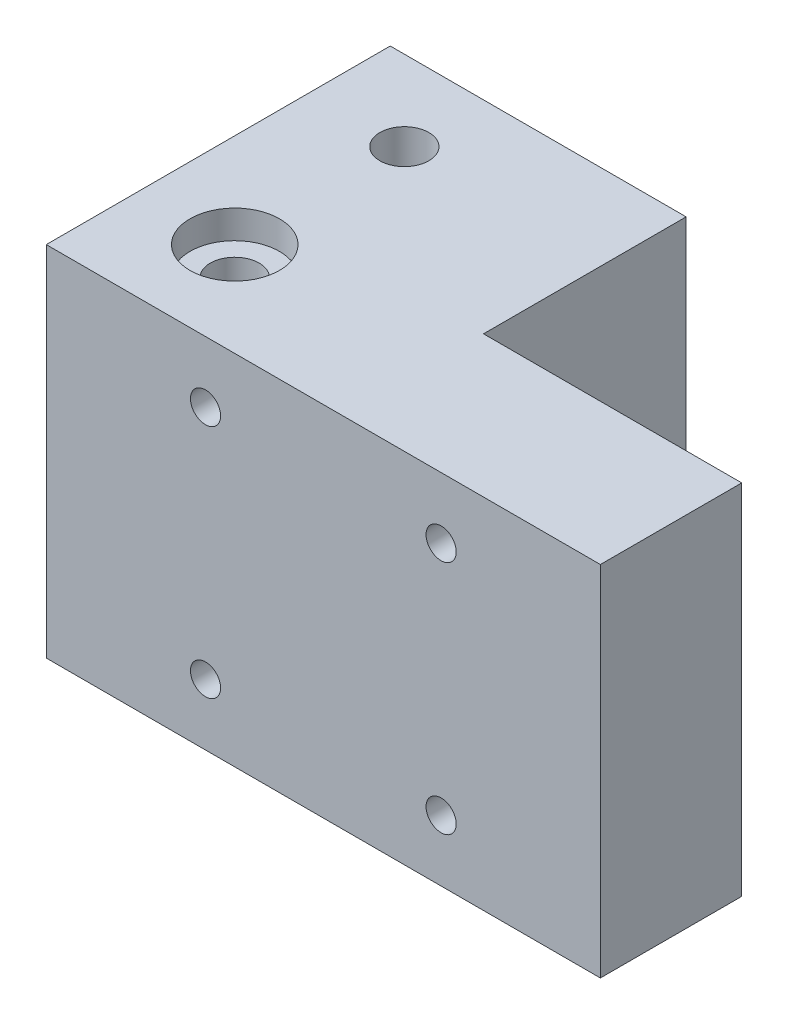
SolidWorks part; units mm, degrees
ref_plane "前视基准面" through (0, 0, 0) normal (0, 0, 1) x (1, 0, 0)
ref_plane "上视基准面" through (0, 0, 0) normal (0, 1, 0) x (1, 0, 0)
ref_plane "右视基准面" through (0, 0, 0) normal (1, 0, 0) x (0, 0, -1)
sketch "草图1" plane through (0, 0, 0) normal (0, 0, 1) x (1, 0, 0)
  line L1 (-30.1396, 19.0453) -> (28.6604, 19.0453)
  line L2 (-30.1396, 19.0453) -> (-30.1396, -12.9547)
  line L3 (-30.1396, -12.9547) -> (28.6604, -12.9547)
  line L4 (28.6604, 19.0453) -> (28.6604, -12.9547)
  dimension "D1" = 58.8
  dimension "D2" = 32
extrude "凸台-拉伸1" add sketch "草图1" along normal blind 41.5
sketch "草图2" plane through (0, 0, 0) normal (0, 0, -1) x (-1, 0, 0)
  line L0 (0.7396, 22.9513) -> (0.7396, -20.038)
  line L1 (42.4969, 3.0453) -> (-36.3492, 3.0453)
  line L2 (-33.9501, -9.4547) -> (38.801, -9.4547)
  line L3 (-33.9501, 15.5453) -> (36.9207, 15.5453)
  line L4 (13.2396, -16.5366) -> (13.2396, 23.8591)
  line L5 (-11.7604, -18.0927) -> (-11.7604, 23.4052)
  dimension "D1" = 12.5
  dimension "D2" = 12.5
  dimension "D3" = 12.5
  dimension "D4" = 12.5
hole_wizard "孔1" positions "3D草图1" profile "草图3" legacy end condition through all
sketch3d "3D草图1"
  line L0 (33.9501, 15.5453, 0) -> (-36.9207, 15.5453, 0) construction
  line L1 (11.7604, -18.0927, 0) -> (11.7604, 23.4052, 0) construction
  line L2 (-13.2396, -16.5366, 0) -> (-13.2396, 23.8591, 0) construction
  line L3 (33.9501, -9.4547, 0) -> (-38.801, -9.4547, 0) construction
  point P0 (11.7604, 15.5453, 0)
  point P6 (-13.2396, 15.5453, 0)
  point P10 (-13.2396, -9.4547, 0)
  point P14 (11.7604, -9.4547, 0)
sketch "草图3" plane through (11.7604, 15.5453, 0) normal (1, 0, 0) x (0, 1, 0)
  line L0 (0, 0) -> (0, 41.5)
  line L1 (0, 41.5) -> (1.6, 41.5)
  line L2 (1.6, 41.5) -> (1.6, 32.5)
  line L3 (1.6, 32.5) -> (3, 32.5)
  line L4 (3, 32.5) -> (3, 0)
  line L5 (3, 0) -> (0, 0)
  line L6 (0, 110) -> (0, -10) construction
  dimension "直径" = 3.2
  dimension "深度" = 41.5
  dimension "柱坑直径" = 6
  dimension "柱坑深度" = 32.5
sketch "草图8" plane through (0, 19.0453, 0) normal (0, 1, 0) x (1, 0, 0)
  circle A0 centre (-0.7396, -31.5) radius 2.6
  dimension "D2" = 5.2
extrude "切除-拉伸6" cut sketch "草图8" against normal blind 33.5
sketch "草图10" plane through (0, -12.9547, 0) normal (0, -1, 0) x (1, 0, 0)
  line L4 (-30.1396, 0) -> (28.6604, 0)
  line L5 (28.6604, 0) -> (28.6604, 41.5)
  line L6 (28.6604, 41.5) -> (-30.1396, 41.5)
  line L7 (-30.1396, 41.5) -> (-30.1396, 0)
  line L8 (-30.1396, 0) -> (28.6604, 0)
  line L9 (28.6604, 0) -> (28.6604, 41.5)
  line L10 (28.6604, 41.5) -> (-30.1396, 41.5)
  line L11 (-30.1396, 41.5) -> (-30.1396, 0)
  dimension "D1" = 0
extrude "凸台-拉伸2" add sketch "草图10" along normal blind 3
sketch "草图18" plane through (0, -12.9547, 0) normal (0, 1, 0) x (1, 0, 0)
  circle A1 centre (-0.7396, -31.5) radius 2.6
  circle A3 centre (-0.7396, -31.5) radius 2.6
  dimension "D1" = 0
extrude "切除-拉伸14" cut sketch "草图18" against normal through all contours A3
sketch "草图19" plane through (0, 0, 0) normal (0, 0, -1) x (-1, 0, 0)
  line L0 (-28.6604, -0.9547) -> (30.1396, -0.9547)
  line L1 (-28.6604, -15.9547) -> (-28.6604, 19.0453) construction
  line L2 (30.1396, 19.0453) -> (30.1396, -15.9547) construction
  line L3 (10.1396, 19.0453) -> (10.1396, -15.9547)
  line L4 (-28.6604, 19.0453) -> (30.1396, 19.0453) construction
  line L5 (30.1396, -15.9547) -> (-28.6604, -15.9547) construction
  line L6 (10.1396, 19.0453) -> (30.1396, 19.0453)
  line L7 (30.1396, 19.0453) -> (30.1396, -0.9547)
  circle M4 centre (13.2396, 15.5453) radius 3
  line M7 (30.1396, -15.9547) -> (30.1396, 19.0453)
  line M8 (30.1396, 19.0453) -> (-28.6604, 19.0453)
  dimension "D1" = 20
  dimension "D2" = 20
extrude "切除-拉伸15" cut sketch "草图19" against normal blind 22 contours L3 L0 M8 M7 M4
sketch "草图20" plane through (0, 0, 0) normal (0, 0, -1) x (-1, 0, 0)
  line L6 (30.1396, -15.9547) -> (30.1396, -0.9547)
  line L7 (30.1396, -0.9547) -> (10.1396, -0.9547)
  line L8 (10.1396, -0.9547) -> (10.1396, 19.0453)
  line L9 (10.1396, 19.0453) -> (-28.6604, 19.0453)
  line L10 (-28.6604, 19.0453) -> (-28.6604, -15.9547)
  line L11 (-28.6604, -15.9547) -> (30.1396, -15.9547)
  line L12 (30.1396, -15.9547) -> (30.1396, -0.9547)
  line L13 (30.1396, -0.9547) -> (10.1396, -0.9547)
  line L14 (10.1396, -0.9547) -> (10.1396, 19.0453)
  line L15 (10.1396, 19.0453) -> (-28.6604, 19.0453)
  line L16 (-28.6604, 19.0453) -> (-28.6604, -15.9547)
  line L17 (-28.6604, -15.9547) -> (30.1396, -15.9547)
  circle A0 centre (13.2396, -9.4547) radius 3 construction
  circle A1 centre (-11.7604, -9.4547) radius 3 construction
  circle A2 centre (-11.7604, 15.5453) radius 3 construction
  circle A3 centre (13.2396, -9.4547) radius 3
  circle A4 centre (-11.7604, -9.4547) radius 3
  circle A5 centre (-11.7604, 15.5453) radius 3
  dimension "D1" = 0
extrude "切除-拉伸16" cut sketch "草图20" against normal blind 5
sketch "草图21" plane through (0, -15.9547, 0) normal (0, -1, 0) x (1, 0, 0)
  line L0 (-30.1396, 19.2146) -> (-17.0647, 5)
  line L1 (-30.1396, 41.5) -> (-30.1396, 5) construction
  line L2 (28.6604, 5) -> (-30.1396, 5) construction
  line L3 (-17.0647, 5) -> (-30.1396, 5)
  line L4 (-30.1396, 5) -> (-30.1396, 19.2146)
extrude "切除-拉伸17" cut sketch "草图21" against normal blind 6
sketch "草图22" plane through (0, 19.0453, 0) normal (0, 1, 0) x (1, 0, 0)
  line L0 (1.2604, -26.5) -> (1.2604, -5)
  line L1 (28.6604, -41.5) -> (-30.1396, -41.5) construction
  line L2 (-10.1396, -5) -> (28.6604, -5) construction
  line L3 (28.6604, -41.5) -> (28.6604, -5) construction
  line L4 (1.2604, -26.5) -> (28.6604, -26.5)
  line L6 (1.2604, -5) -> (28.6604, -5)
  line L7 (28.6604, -5) -> (28.6604, -26.5)
  dimension "D1" = 27.4
  dimension "D2" = 15
extrude "切除-拉伸18" cut sketch "草图22" against normal through all
sketch "草图23" plane through (0, -0.9547, 0) normal (0, 1, 0) x (1, 0, 0)
  circle A0 centre (-20.1396, -13.5) radius 2.6
  dimension "D1" = 5.2
extrude "切除-拉伸19" cut sketch "草图23" against normal through all
sketch "草图24" plane through (0, -15.9547, 0) normal (0, -1, 0) x (-1, 0, 0)
  line L0 (22.7396, -13.5) -> (20.1396, -13.5)
  line L1 (20.1396, -13.5) -> (20.1396, -16.1)
  line L2 (24.6313, -13.2261) -> (20.7871, -9.0468)
  line L3 (17.0647, -5) -> (30.1396, -19.2146) construction
  circle A0 centre (20.1396, -13.5) radius 2.6 construction
  arc A1 (20.7871, -9.0468) -> (24.6313, -13.2261) centre (20.1396, -13.5) ccw
  circle M1 centre (20.1396, -13.5) radius 2.6
  line M6 (30.1396, -19.2146) -> (17.0647, -5)
  dimension "D1" = 9
extrude "切除-拉伸20" cut sketch "草图24" against normal blind 6 contours A1 M6 M1
sketch "草图25" plane through (0, -0.9547, 0) normal (0, 1, 0) x (1, 0, 0)
  line L4 (-10.1396, -5) -> (-30.1396, -5)
  line L5 (-30.1396, -5) -> (-30.1396, -22)
  line L6 (-30.1396, -22) -> (-10.1396, -22)
  line L7 (-10.1396, -22) -> (-10.1396, -5)
  line L8 (-10.1396, -5) -> (-30.1396, -5)
  line L9 (-30.1396, -5) -> (-30.1396, -22)
  line L10 (-30.1396, -22) -> (-10.1396, -22)
  line L11 (-10.1396, -22) -> (-10.1396, -5)
  circle A0 centre (-20.1396, -13.5) radius 2.6 construction
  circle A1 centre (-20.1396, -13.5) radius 2.6
  dimension "D1" = 0
extrude "切除-拉伸21" cut sketch "草图25" against normal blind 0.1
sketch "草图27" plane through (-10.1396, 0, 0) normal (-1, 0, 0) x (0, 0, 1)
  line L4 (5, 19.0453) -> (5, -1.0547)
  line L5 (5, -1.0547) -> (22, -1.0547)
  line L6 (22, -1.0547) -> (22, 19.0453)
  line L7 (22, 19.0453) -> (5, 19.0453)
  line L8 (5, 19.0453) -> (5, -1.0547)
  line L9 (5, -1.0547) -> (22, -1.0547)
  line L10 (22, -1.0547) -> (22, 19.0453)
  line L11 (22, 19.0453) -> (5, 19.0453)
  dimension "D1" = 0
extrude "切除-拉伸22" cut sketch "草图27" against normal blind 0.1
sketch "草图28" plane through (-10.0396, 0, 0) normal (-1, 0, 0) x (0, 0, 1)
  circle A0 centre (13.5, 8.9953) radius 2.6
  dimension "D1" = 5.2
extrude "切除-拉伸23" cut sketch "草图28" against normal through all contours A0
sketch "草图29" plane through (1.2604, 0, 0) normal (1, 0, 0) x (0, 0, -1)
  circle A1 centre (-13.5, 8.9953) radius 4.5
  circle A2 centre (-13.5, 8.9953) radius 2.6 construction
  circle A3 centre (-13.5, 8.9953) radius 2.6
  dimension "D1" = 9
extrude "切除-拉伸24" cut sketch "草图29" against normal blind 5 contours A1 | A3
sketch "草图30" plane through (0, 19.0453, 0) normal (0, 1, 0) x (1, 0, 0)
  circle A0 centre (-20.1396, -31.5) radius 2.6
  dimension "D3" = 5.2
extrude "切除-拉伸25" cut sketch "草图30" against normal through all
sketch "草图31" plane through (0, 19.0453, 0) normal (0, 1, 0) x (1, 0, 0)
  circle A0 centre (-0.7396, -31.5) radius 2.6 construction
  circle A1 centre (-0.7396, -31.5) radius 2.6
extrude "凸台-拉伸3" add sketch "草图31" against normal through all
sketch "草图32" plane through (0, -1.0547, 0) normal (0, 1, 0) x (1, 0, 0)
  line L4 (-30.1396, -22) -> (-10.0396, -22)
  line L5 (-10.0396, -22) -> (-10.0396, -5)
  line L6 (-10.0396, -5) -> (-30.1396, -5)
  line L7 (-30.1396, -5) -> (-30.1396, -22)
  line L8 (-30.1396, -22) -> (-10.0396, -22)
  line L9 (-10.0396, -22) -> (-10.0396, -5)
  line L10 (-10.0396, -5) -> (-30.1396, -5)
  line L11 (-30.1396, -5) -> (-30.1396, -22)
  circle A1 centre (-20.1396, -13.5) radius 2.6
  circle A2 centre (-20.1396, -13.5) radius 2.6
  dimension "D1" = 0
  dimension "D2" = 0
extrude "切除-拉伸26" cut sketch "草图32" against normal blind 7
sketch "草图33" plane through (0, 0, 22) normal (0, 0, -1) x (-1, 0, 0)
  line L0 (10.0396, 12.0453) -> (30.1396, 12.0453)
  line L1 (10.0396, -8.0547) -> (10.0396, 19.0453) construction
  line L2 (30.1396, -8.0547) -> (30.1396, 19.0453) construction
  line L3 (30.1396, 19.0453) -> (10.0396, 19.0453) construction
  line L4 (10.0396, 12.0453) -> (10.0396, 19.0453)
  line L5 (10.0396, 19.0453) -> (30.1396, 19.0453)
  line L6 (30.1396, 19.0453) -> (30.1396, 12.0453)
  circle A0 centre (13.2396, 15.5453) radius 3 construction
  circle A1 centre (13.2396, 15.5453) radius 3
  dimension "D1" = 7
extrude "凸台-拉伸4" add sketch "草图33" along normal blind 17
sketch "草图34" plane through (-3.7396, 0, 0) normal (1, 0, 0) x (0, 0, -1)
  circle A1 centre (-13.5, 8.9953) radius 4.5
  circle A2 centre (-13.5, 8.9953) radius 4.5
  dimension "D1" = 0
extrude "凸台-拉伸5" add sketch "草图34" along normal blind 5
sketch "草图35" plane through (-3.7396, 0, 0) normal (-1, 0, 0) x (0, 0, 1)
  circle A1 centre (13.5, 8.9953) radius 2.6
  circle A2 centre (13.5, 8.9953) radius 2.6
  dimension "D1" = 0
extrude "凸台-拉伸6" add sketch "草图35" along normal blind 6.3
sketch "草图39" plane through (0, 12.0453, 0) normal (0, -1, 0) x (1, 0, 0)
  circle A0 centre (-20.1396, 13.5) radius 2.6 construction
  circle A1 centre (-20.1396, 13.5) radius 2.6
extrude "切除-拉伸29" cut sketch "草图39" against normal through all
sketch "草图40" plane through (0, 12.0453, 0) normal (0, -1, 0) x (1, 0, 0)
  line L4 (-10.0396, 22) -> (-30.1396, 22)
  line L5 (-30.1396, 22) -> (-30.1396, 5)
  line L6 (-30.1396, 5) -> (-10.0396, 5)
  line L7 (-10.0396, 5) -> (-10.0396, 22)
  line L8 (-10.0396, 22) -> (-30.1396, 22)
  line L9 (-30.1396, 22) -> (-30.1396, 5)
  line L10 (-30.1396, 5) -> (-10.0396, 5)
  line L11 (-10.0396, 5) -> (-10.0396, 22)
  circle A0 centre (-20.1396, 13.5) radius 2.6 construction
  circle A1 centre (-20.1396, 13.5) radius 2.6
  dimension "D1" = 0
extrude "凸台-拉伸7" add sketch "草图40" along normal blind 7.9
sketch "草图41" plane through (0, -8.0547, 0) normal (0, 1, 0) x (1, 0, 0)
  line L0 (-10.0396, -22) -> (-30.1396, -22)
  line L1 (-30.1396, -22) -> (-30.1396, -5)
  line L2 (-30.1396, -5) -> (-10.0396, -5)
  line L3 (-10.0396, -5) -> (-10.0396, -22)
extrude "切除-拉伸30" cut sketch "草图41" against normal blind 7.9
sketch "草图42" plane through (-10.0396, 0, 0) normal (-1, 0, 0) x (0, 0, 1)
  circle A0 centre (13.5, -5.8547) radius 2.6
  dimension "D2" = 5.2
extrude "切除-拉伸31" cut sketch "草图42" against normal through all
sketch "草图43" plane through (1.2604, 0, 0) normal (1, 0, 0) x (0, 0, -1)
  circle A0 centre (-13.5, -5.8547) radius 4.5
  circle A1 centre (-13.5, -5.8547) radius 2.6 construction
  circle A2 centre (-13.5, -5.8547) radius 2.6
  dimension "D1" = 9
extrude "切除-拉伸32" cut sketch "草图43" against normal blind 5.2
sketch "草图44" plane through (0, 19.0453, 0) normal (0, 1, 0) x (1, 0, 0)
  line L6 (1.2604, -5) -> (-30.1396, -5)
  line L7 (-30.1396, -5) -> (-30.1396, -41.5)
  line L8 (-30.1396, -41.5) -> (28.6604, -41.5)
  line L9 (28.6604, -41.5) -> (28.6604, -26.5)
  line L10 (28.6604, -26.5) -> (1.2604, -26.5)
  line L11 (1.2604, -26.5) -> (1.2604, -5)
  line L12 (1.2604, -5) -> (-30.1396, -5)
  line L13 (-30.1396, -5) -> (-30.1396, -41.5)
  line L14 (-30.1396, -41.5) -> (28.6604, -41.5)
  line L15 (28.6604, -41.5) -> (28.6604, -26.5)
  line L16 (28.6604, -26.5) -> (1.2604, -26.5)
  line L17 (1.2604, -26.5) -> (1.2604, -5)
  circle A0 centre (-20.1396, -13.5) radius 2.6 construction
  circle A1 centre (-20.1396, -31.5) radius 2.6 construction
  circle A2 centre (-20.1396, -13.5) radius 2.6
  circle A3 centre (-20.1396, -31.5) radius 2.6
  dimension "D1" = 0
extrude "凸台-拉伸8" add sketch "草图44" along normal blind 3
sketch "草图46" plane through (0, 22.0453, 0) normal (0, 1, 0) x (1, 0, 0)
  circle A0 centre (-20.1396, -31.5) radius 4.75
  circle A1 centre (-20.1396, -31.5) radius 2.6 construction
  circle A2 centre (-20.1396, -31.5) radius 2.6
  dimension "D1" = 9.5
extrude "切除-拉伸33" cut sketch "草图46" against normal blind 3
